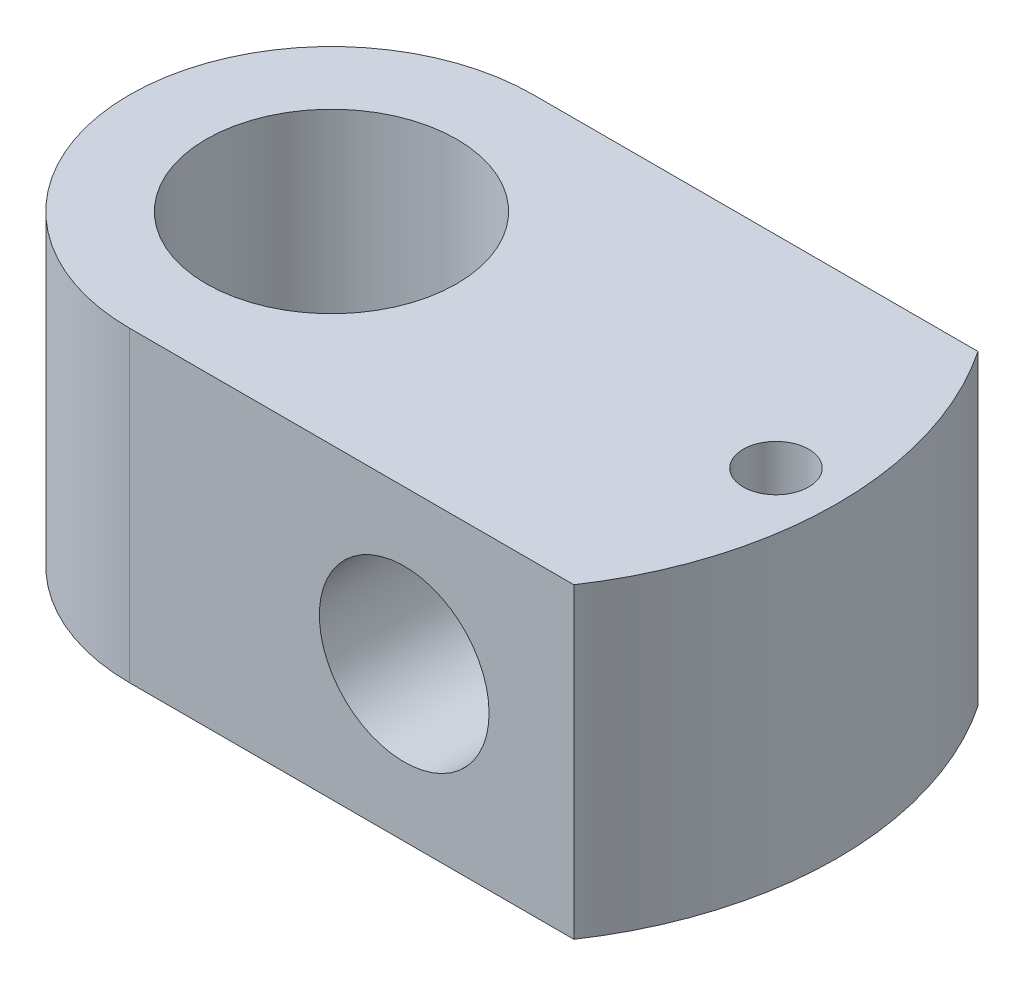
SolidWorks part; units mm, degrees
material "Nylon 101"
ref_plane "Front Plane" through (0, 0, 0) normal (0, 0, 1) x (1, 0, 0)
ref_plane "Top Plane" through (0, 0, 0) normal (0, 1, 0) x (1, 0, 0)
ref_plane "Right Plane" through (0, 0, 0) normal (1, 0, 0) x (0, 0, -1)
sketch "Sketch1" plane through (0, 0, 0) normal (0, 1, 0) x (1, 0, 0)
  line L0 (0, 31.75) -> (69.85, 31.75)
  line L1 (0, -31.75) -> (69.85, -31.75)
  arc A0 (0, 31.75) -> (0, -31.75) centre (0, 0) ccw
  arc A1 (69.85, 31.75) -> (69.85, -31.75) centre (22.4556, 0) cw
  point P7 (-31.75, 0)
  point P8 (79.502, 0)
  dimension "D1" = 63.5
  dimension "D2" = 111.252
  dimension "D3" = 69.85
extrude "Boss-Extrude1" add sketch "Sketch1" along normal mid plane 48.26
sketch "Sketch2" plane through (0, 24.13, 0) normal (0, 1, 0) x (1, 0, 0)
  circle A0 centre (0, 0) radius 19.685
  dimension "D1" = 39.37
extrude "Cut-Extrude1" cut sketch "Sketch2" against normal through all
sketch "Sketch3" plane through (0, 0, 31.75) normal (0, 0, 1) x (1, 0, 0)
  line L0 (-31.75, 24.13) -> (-31.75, -24.13) construction
  circle A0 centre (43.18, 0) radius 13.335
  point P2 (-31.75, 0)
  dimension "D1" = 26.67
  dimension "D2" = 74.93
extrude "Cut-Extrude2" cut sketch "Sketch3" against normal through all
sketch "Sketch4" plane through (0, 24.13, 0) normal (0, 1, 0) x (1, 0, 0)
  circle A0 centre (69.85, 0) radius 5.1435
  dimension "D1" = 10.287
extrude "Cut-Extrude3" cut sketch "Sketch4" against normal through all
